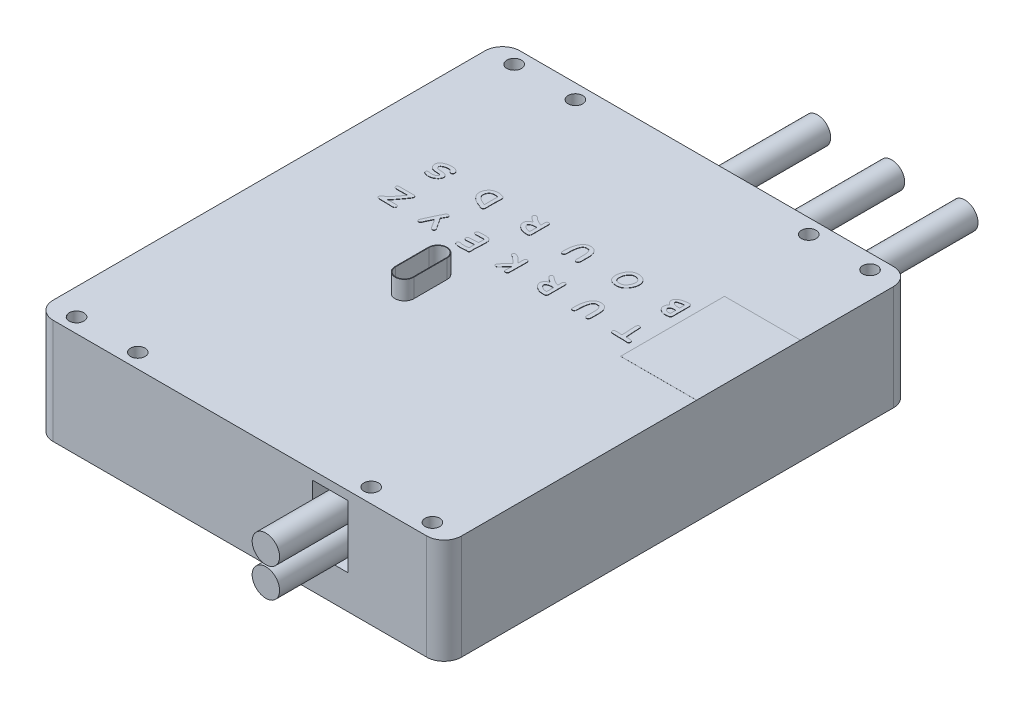
SolidWorks part; units mm, degrees
ref_plane "Front Plane" through (0, 0, 0) normal (0, 0, 1) x (1, 0, 0)
ref_plane "Top Plane" through (0, 0, 0) normal (0, 1, 0) x (1, 0, 0)
ref_plane "Right Plane" through (0, 0, 0) normal (1, 0, 0) x (0, 0, -1)
sketch "Sketch1" plane through (0, 0, 0) normal (0, 1, 0) x (1, 0, 0)
  line L0 (4.5, 2.5) -> (65.5, 2.5) construction
  line L1 (3, 0) -> (67, 0)
  line L2 (0, 3) -> (0, 77)
  line L3 (3, 80) -> (67, 80)
  line L4 (70, 3) -> (70, 77)
  line L5 (4.7907, 77.5) -> (63.4798, 77.5) construction
  line L6 (0, 40) -> (70, 40) construction
  arc A0 (3, 0) -> (0, 3) centre (3, 3) cw
  arc A1 (67, 0) -> (70, 3) centre (67, 3) ccw
  arc A2 (67, 80) -> (70, 77) centre (67, 77) cw
  arc A3 (0, 77) -> (3, 80) centre (3, 77) cw
  circle A4 centre (4.5, 2.5) radius 1.25
  circle A5 centre (15, 2.5) radius 1.25
  circle A6 centre (55, 2.5) radius 1.25
  circle A7 centre (65.5, 2.5) radius 1.25
  circle A8 centre (65.5, 77.5) radius 1.25
  circle A9 centre (55, 77.5) radius 1.25
  circle A10 centre (15, 77.5) radius 1.25
  circle A11 centre (4.5, 77.5) radius 1.25
  point P7 (0, 0)
  point P12 (70, 80)
  point P15 (0, 80)
  point P20 (15, 2.5)
  point P21 (55, 2.5)
  dimension "D3" = 3
  dimension "D10" = 2.5
  dimension "D1" = 70
  dimension "D2" = 80
  dimension "D4" = 75
  dimension "D5" = 2.5
  dimension "D6" = 61
  dimension "D7" = 4.5
  dimension "D8" = 40
  dimension "D9" = 15
extrude "Boss-Extrude1" add sketch "Sketch1" along normal blind 18
sketch "Sketch2" plane through (0, 18, 0) normal (0, 1, 0) x (1, 0, 0)
  line L0 (55.8139, 49.3411) -> (12.4879, 49.3411) construction
  text T0 "<b>TURKEYZ</b>\r\n<b>BOURDS</b>" font "Comic Sans MS" height 3.5
extrude "Boss-Extrude2" add sketch "Sketch2" along normal blind 0.05
sketch "Sketch4" plane through (0, 18, 0) normal (0, 1, 0) x (1, 0, 0)
  line L0 (29.1, 39.8) -> (29.1, 34.1) construction
  line L1 (30.7, 39.8) -> (30.7, 34.1)
  line L2 (27.5, 39.8) -> (27.5, 34.1)
  line L3 (29.1, 39.8) -> (29.1, 34.1) construction
  line L4 (30.6, 39.8) -> (30.6, 34.1)
  line L5 (27.6, 39.8) -> (27.6, 34.1)
  line L6 (0, 77) -> (0, 3) construction
  line L7 (67, 80) -> (3, 80) construction
  arc A0 (30.7, 39.8) -> (27.5, 39.8) centre (29.1, 39.8) ccw
  arc A1 (27.5, 34.1) -> (30.7, 34.1) centre (29.1, 34.1) ccw
  arc A2 (30.6, 39.8) -> (27.6, 39.8) centre (29.1, 39.8) ccw
  arc A3 (27.6, 34.1) -> (30.6, 34.1) centre (29.1, 34.1) ccw
  point P2 (29.1, 36.95)
  point P7 (29.1, 36.95)
  point P14 (29.1, 41.3)
  point P15 (29.1, 32.6)
  point P18 (29.1, 32.5)
  dimension "D1" = 8.7
  dimension "D2" = 3
  dimension "D3" = 0.1
  dimension "D4" = 27.5
  dimension "D5" = 47.5
extrude "Boss-Extrude3" add sketch "Sketch4" along normal blind 3.2
sketch "Sketch5" plane through (0, 18, 0) normal (0, 1, 0) x (1, 0, 0)
  line L0 (70, 3) -> (70, 77) construction
  line L1 (70, 61.0819) -> (56.9749, 61.0819)
  line L2 (70, 61.0819) -> (70, 43.2761)
  line L3 (70, 43.2761) -> (56.9749, 43.2761)
  line L4 (56.9749, 61.0819) -> (56.9749, 43.2761)
extrude "Boss-Extrude4" add sketch "Sketch5" along normal blind 0.01
sketch "Sketch6" plane through (0, 0, 0) normal (0, 0, 1) x (1, 0, 0)
  line L0 (3, 18) -> (67, 18) construction
  line L1 (53.5, 16.5) -> (47.4, 16.5)
  line L2 (53.5, 16.5) -> (53.5, 5.8)
  line L3 (53.5, 5.8) -> (47.4, 5.8)
  line L4 (47.4, 16.5) -> (47.4, 5.8)
  line L5 (70, 18) -> (70, 0) construction
  point P6 (53.5, 11.15)
  dimension "D1" = 1.5
  dimension "D2" = 6.1
  dimension "D3" = 16.5
  dimension "D4" = 10.7
extrude "Cut-Extrude1" cut sketch "Sketch6" against normal blind 7.1
sketch "Sketch7" plane through (0, 0, -7.1) normal (0, 0, 1) x (1, 0, 0)
  line L0 (47.4, 5.8) -> (53.5, 5.8) construction
  circle A0 centre (50.45, 8.3) radius 2.35
  circle A1 centre (50.45, 13.3) radius 2.35
  dimension "D1" = 4.7
  dimension "D2" = 4.7
  dimension "D4" = 5
  dimension "D3" = 2.5
extrude "Boss-Extrude5" add sketch "Sketch7" along normal blind 18.1
sketch "Sketch8" plane through (0, 0, -80) normal (0, 0, -1) x (-1, 0, 0)
  line L0 (-31.1789, 16.5) -> (-63.5, 16.5) construction
  line L1 (-67, 18) -> (-3, 18) construction
  line L2 (-70, 18) -> (-70, 0) construction
  line L4 (-63.5, 16.5) -> (-57.5, 16.5)
  line L5 (-63.5, 16.5) -> (-63.5, 9)
  line L6 (-63.5, 9) -> (-57.5, 9)
  line L7 (-57.5, 16.5) -> (-57.5, 9)
  line L8 (-51, 16.5) -> (-45, 16.5)
  line L9 (-51, 16.5) -> (-51, 9)
  line L10 (-51, 9) -> (-45, 9)
  line L11 (-45, 16.5) -> (-45, 9)
  line L12 (-38.5, 16.5) -> (-32.5, 16.5)
  line L13 (-38.5, 16.5) -> (-38.5, 9)
  line L14 (-38.5, 9) -> (-32.5, 9)
  line L15 (-32.5, 16.5) -> (-32.5, 9)
  dimension "D1" = 1.5
  dimension "D2" = 6.5
  dimension "D3" = 6
  dimension "D4" = 6
  dimension "D5" = 6
  dimension "D6" = 6.5
  dimension "D7" = 6.5
  dimension "D8" = 31
extrude "Cut-Extrude2" cut sketch "Sketch8" against normal blind 18.1
sketch "Sketch9" plane through (0, 0, -61.9) normal (0, 0, -1) x (-1, 0, 0)
  line L0 (-63.5, 12.75) -> (-33.5421, 12.75) construction
  line L1 (-63.5, 16.5) -> (-63.5, 9) construction
  circle A0 centre (-60.2587, 12.75) radius 2.25
  circle A1 centre (-47.7201, 12.4679) radius 2.22
  circle A2 centre (-35.0053, 12.75) radius 2.25
extrude "Boss-Extrude6" add sketch "Sketch9" along normal blind 37.1
